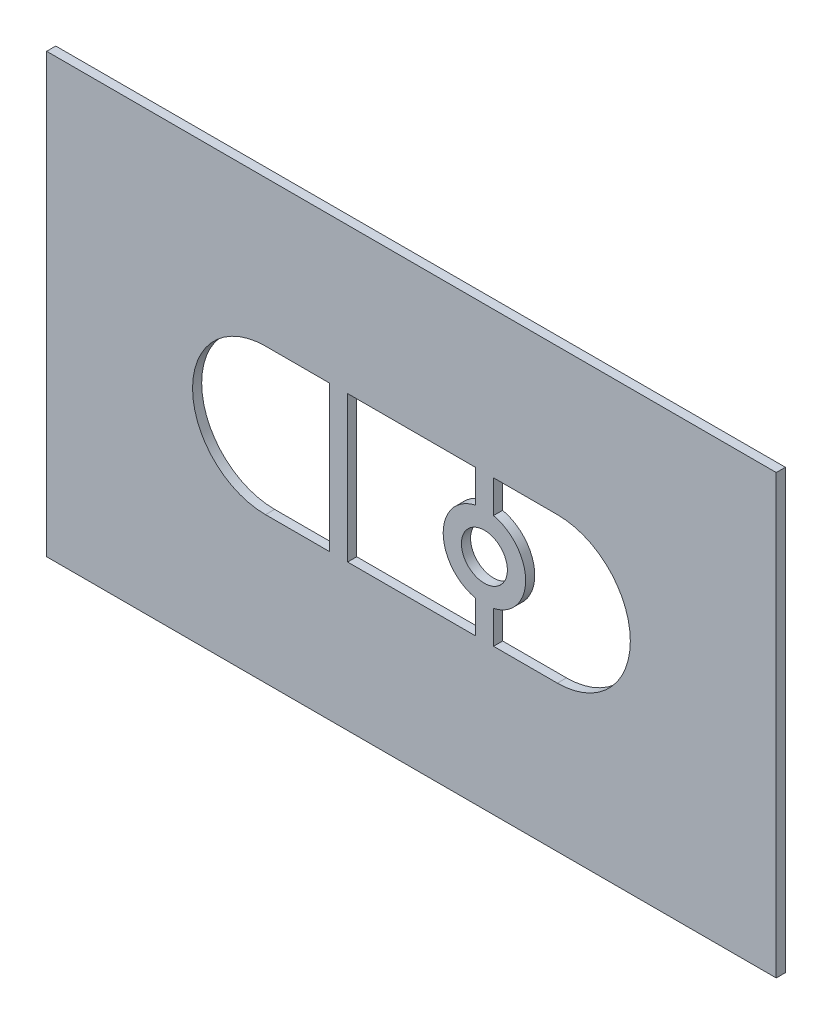
SolidWorks part; units mm, degrees
material "Thornel Mat VMA"
ref_plane "Front Plane" through (0, 0, 0) normal (0, 0, 1) x (1, 0, 0)
ref_plane "Top Plane" through (0, 0, 0) normal (0, 1, 0) x (1, 0, 0)
ref_plane "Right Plane" through (0, 0, 0) normal (1, 0, 0) x (0, 0, -1)
sketch "Sketch1" plane through (0, 0, 0) normal (0, 0, 1) x (1, 0, 0)
  line L0 (0, 38.1) -> (127, 38.1) construction
  line L1 (0, 0) -> (127, 0)
  line L2 (0, 0) -> (0, 76.2)
  line L3 (0, 76.2) -> (127, 76.2)
  line L4 (127, 0) -> (127, 76.2)
  line L5 (38.1, 50.8) -> (49.2125, 50.8)
  line L6 (88.9, 25.4) -> (77.7875, 25.4)
  line L7 (49.2125, 50.8) -> (49.2125, 25.4)
  line L8 (52.3875, 50.8) -> (74.6125, 50.8)
  line L9 (52.3875, 25.4) -> (52.3875, 50.8)
  line L10 (74.6125, 50.8) -> (74.6125, 45.0972)
  line L11 (49.2125, 25.4) -> (38.1, 25.4)
  line L12 (77.7875, 50.8) -> (77.7875, 45.0972)
  line L13 (77.7875, 50.8) -> (88.9, 50.8)
  line L14 (74.6125, 25.4) -> (52.3875, 25.4)
  line L15 (74.6125, 38.1) -> (77.7875, 38.1) construction
  line L16 (74.6125, 31.1028) -> (74.6125, 25.4)
  line L17 (77.7875, 31.1028) -> (77.7875, 25.4)
  line L18 (49.2125, 38.1) -> (52.3875, 38.1) construction
  line L19 (49.2125, 38.1) -> (52.3875, 38.1) construction
  arc A0 (38.1, 50.8) -> (38.1, 25.4) centre (38.1, 38.1) ccw
  arc A1 (88.9, 25.4) -> (88.9, 50.8) centre (88.9, 38.1) ccw
  circle A2 centre (76.2, 38.1) radius 4
  arc A3 (74.6125, 45.0972) -> (74.6125, 31.1028) centre (76.2, 38.1) ccw
  arc A4 (77.7875, 31.1028) -> (77.7875, 45.0972) centre (76.2, 38.1) ccw
  point P31 (50.8, 38.1)
  point P32 (0, 0)
  dimension "D3" = 25.4
  dimension "D5" = 50.8
  dimension "D8" = 8
  dimension "D9" = 3.175
  dimension "D1" = 76.2
  dimension "D2" = 127
  dimension "D4" = 38.1
  dimension "D6" = 3.175
  dimension "D7" = 3.175
  dimension "D10" = 12.7
  dimension "D11" = 12.7
extrude "Boss-Extrude1" add sketch "Sketch1" along normal blind 1.5875
